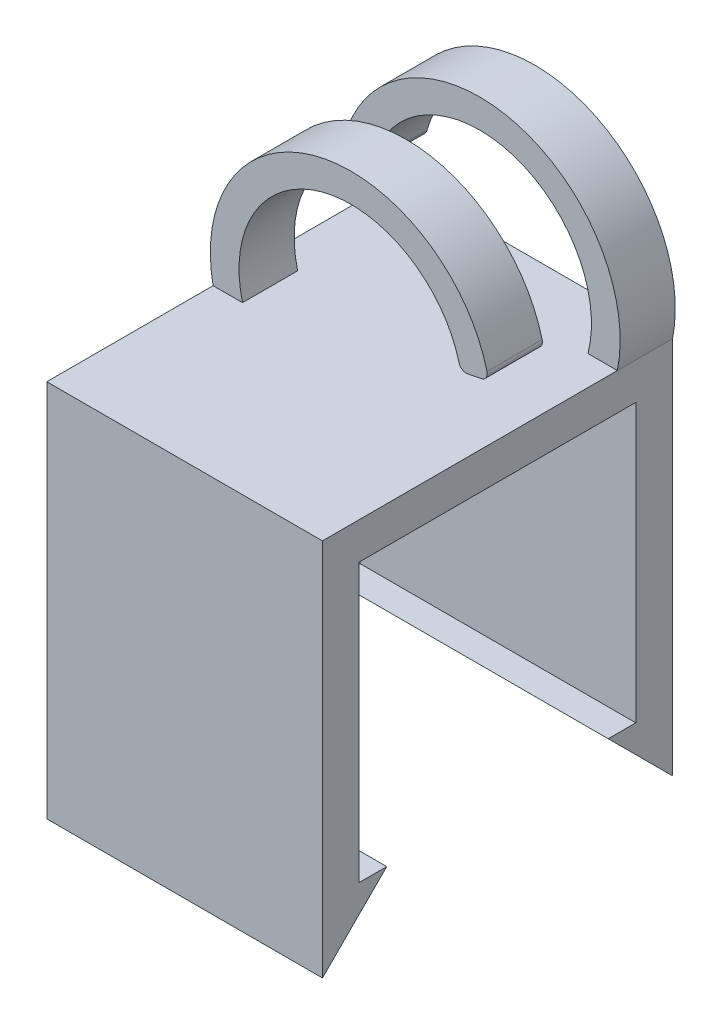
SolidWorks part; units mm, degrees
ref_plane "前视基准面" through (0, 0, 0) normal (0, 0, 1) x (1, 0, 0)
ref_plane "上视基准面" through (0, 0, 0) normal (0, 1, 0) x (1, 0, 0)
ref_plane "右视基准面" through (0, 0, 0) normal (1, 0, 0) x (0, 0, -1)
sketch "草图1" plane through (0, 0, 0) normal (0, 1, 0) x (1, 0, 0)
  line L1 (-15.6296, 6.8648) -> (-0.6296, 6.8648)
  line L2 (-15.6296, 6.8648) -> (-15.6296, -12.1852)
  line L3 (-15.6296, -12.1852) -> (-0.6296, -12.1852)
  line L4 (-0.6296, 6.8648) -> (-0.6296, -12.1852)
  line L5 (-15.6296, 4.8648) -> (-0.6296, 4.8648)
  line L6 (-15.6296, 4.8648) -> (-15.6296, -10.1852)
  line L7 (-15.6296, -10.1852) -> (-0.6296, -10.1852)
  line L8 (-0.6296, 4.8648) -> (-0.6296, -10.1852)
  dimension "D1" = 2
  dimension "D2" = 2
  dimension "D3" = 15.05
  dimension "D4" = 15
extrude "凸台-拉伸1" add sketch "草图1" along normal blind 15.1 contours L2 L5 L4 L1 | L7 L2 L3 L4
sketch "草图2" plane through (0, 15.1, 0) normal (0, 1, 0) x (1, 0, 0)
  line L1 (-15.6296, 6.8648) -> (-0.6296, 6.8648)
  line L2 (-15.6296, 6.8648) -> (-15.6296, -12.1852)
  line L3 (-15.6296, -12.1852) -> (-0.6296, -12.1852)
  line L4 (-0.6296, 6.8648) -> (-0.6296, -12.1852)
extrude "凸台-拉伸2" add sketch "草图2" along normal blind 2
sketch "草图3" plane through (-15.6296, 0, 0) normal (-1, 0, 0) x (0, 0, 1)
  line L0 (-6.8648, 0) -> (-3.3648, 0)
  line L1 (-3.3648, 0) -> (-6.8648, -3.5)
  line L2 (-6.8648, -3.5) -> (-6.8648, 0)
  line L3 (12.1852, 0) -> (8.6852, 0)
  line L4 (8.6852, 0) -> (12.1852, -3.5)
  line L5 (12.1852, -3.5) -> (12.1852, 0)
  dimension "D1" = 3.5
  dimension "D2" = 3.5
  dimension "D3" = 3.5
  dimension "D4" = 3.5
extrude "凸台-拉伸3" add sketch "草图3" against normal blind 15
sketch "草图5" plane through (0, 0, -6.8648) normal (0, 0, -1) x (-1, 0, 0)
  line L0 (15.6296, 17.1) -> (15.6296, 20.1) construction
  line L1 (0.6296, 17.1) -> (15.6296, 17.1) construction
  line L2 (14.5708, 19.8882) -> (15.1222, 19.9985)
  line L3 (15.6296, 20.1) -> (16.5209, 15.6438) construction
  line L4 (2.2296, 17.1) -> (0.6296, 17.1)
  line L5 (8.1296, 17.1) -> (8.1296, 23.9889) construction
  line L6 (15.6296, 17.1) -> (0.6296, 17.1) construction
  arc A0 (0.6296, 17.1) -> (15.5063, 20.6209) centre (8.1296, 18.6) cw
  arc A1 (2.2296, 17.1) -> (13.9913, 20.2435) centre (8.1296, 18.6) cw
  arc A2 (15.5063, 20.6209) -> (15.1222, 19.9985) centre (15.0241, 20.4888) cw
  arc A3 (13.9913, 20.2435) -> (14.5708, 19.8882) centre (14.4727, 20.3785) ccw
  point P21 (0, 0)
  dimension "D2" = 1.6
  dimension "D4" = 0.5
  dimension "D1" = 3
extrude "凸台-拉伸4" add sketch "草图5" against normal blind 3
ref_plane "基准面1" through (0, 0, 0.1352) normal (0, 0, 1) x (1, 0, 0)
sketch "草图7" plane through (0, 0, 0.1352) normal (0, 0, 1) x (1, 0, 0)
  line L0 (-15.6296, 17.1) -> (-0.6296, 17.1) construction
  line L1 (-1.78, 19.8699) -> (-1.0327, 20.0194)
  line L2 (-0.6296, 17.1) -> (-0.6296, 23.1843) construction
  line L3 (-0.6296, 20.1) -> (-0.2082, 17.9928) construction
  line L4 (-15.6296, 17.1) -> (-14.0296, 17.1)
  arc A0 (-15.6296, 17.1) -> (-0.7238, 20.5116) centre (-8.1296, 18.6) cw
  arc A1 (-0.6296, 17.1) -> (-15.5063, 20.6209) centre (-8.1296, 18.6) ccw construction
  arc A2 (-14.0296, 17.1) -> (-2.2451, 20.1597) centre (-8.1296, 18.6) cw
  arc A3 (-2.2296, 17.1) -> (-13.9913, 20.2435) centre (-8.1296, 18.6) ccw construction
  arc A4 (-0.7238, 20.5116) -> (-1.0327, 20.0194) centre (-1.1111, 20.4116) cw
  arc A5 (-2.2451, 20.1597) -> (-1.78, 19.8699) centre (-1.8585, 20.2622) ccw
  point P24 (-2.1602, 19.7939)
  dimension "D2" = 0.4
  dimension "D1" = 1.6
extrude "凸台-拉伸5" add sketch "草图7" along normal blind 3
